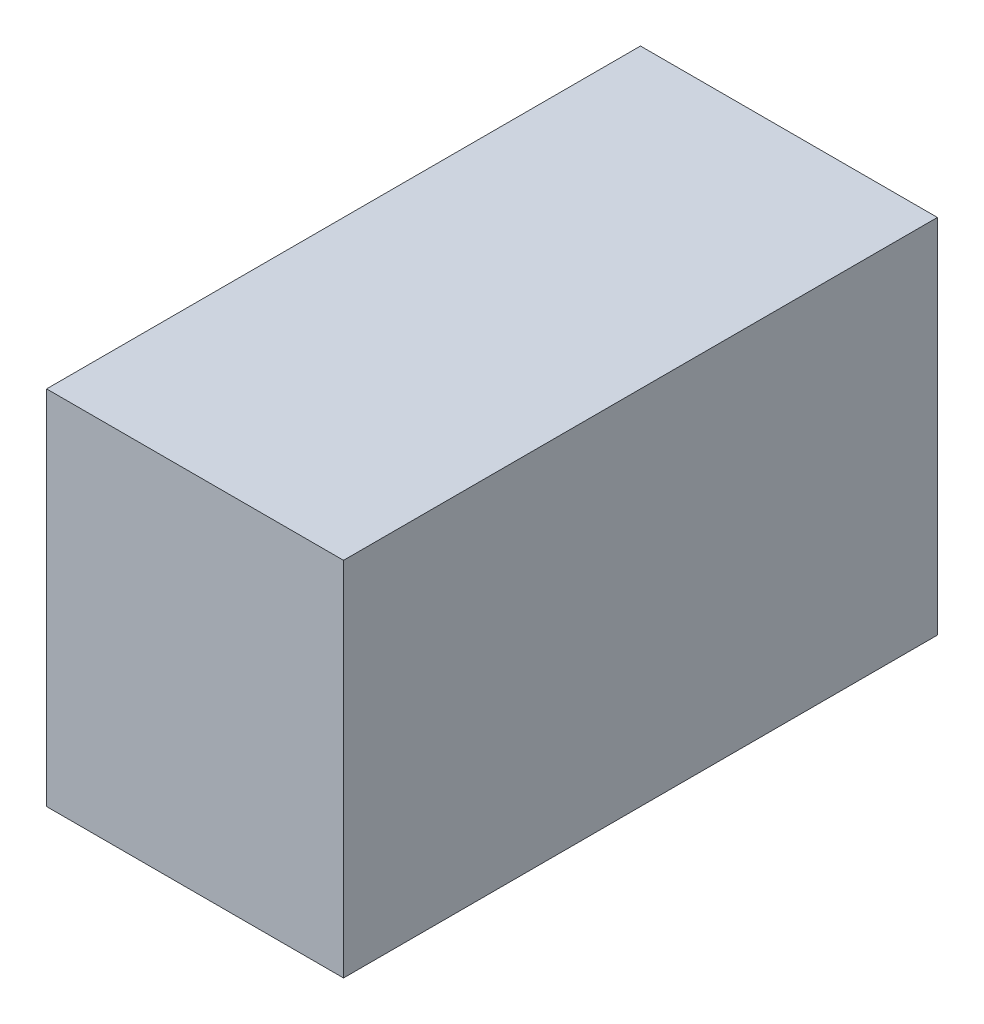
SolidWorks part; units mm, degrees
ref_plane "前视基准面" through (0, 0, 0) normal (0, 0, 1) x (1, 0, 0)
ref_plane "上视基准面" through (0, 0, 0) normal (0, 1, 0) x (1, 0, 0)
ref_plane "右视基准面" through (0, 0, 0) normal (1, 0, 0) x (0, 0, -1)
sketch "草图1" plane through (0, 0, 0) normal (0, 0, 1) x (1, 0, 0)
  line L1 (27.5, 33.5) -> (-27.5, 33.5)
  line L2 (27.5, 33.5) -> (27.5, -33.5)
  line L3 (27.5, -33.5) -> (-27.5, -33.5)
  line L4 (-27.5, 33.5) -> (-27.5, -33.5)
  line L5 (27.5, 33.5) -> (-27.5, -33.5) construction
  line L6 (27.5, -33.5) -> (-27.5, 33.5) construction
  point P0 (0, 0)
  dimension "D1" = 67
  dimension "D2" = 55
extrude "凸台-拉伸1" add sketch "草图1" along normal mid plane 110
